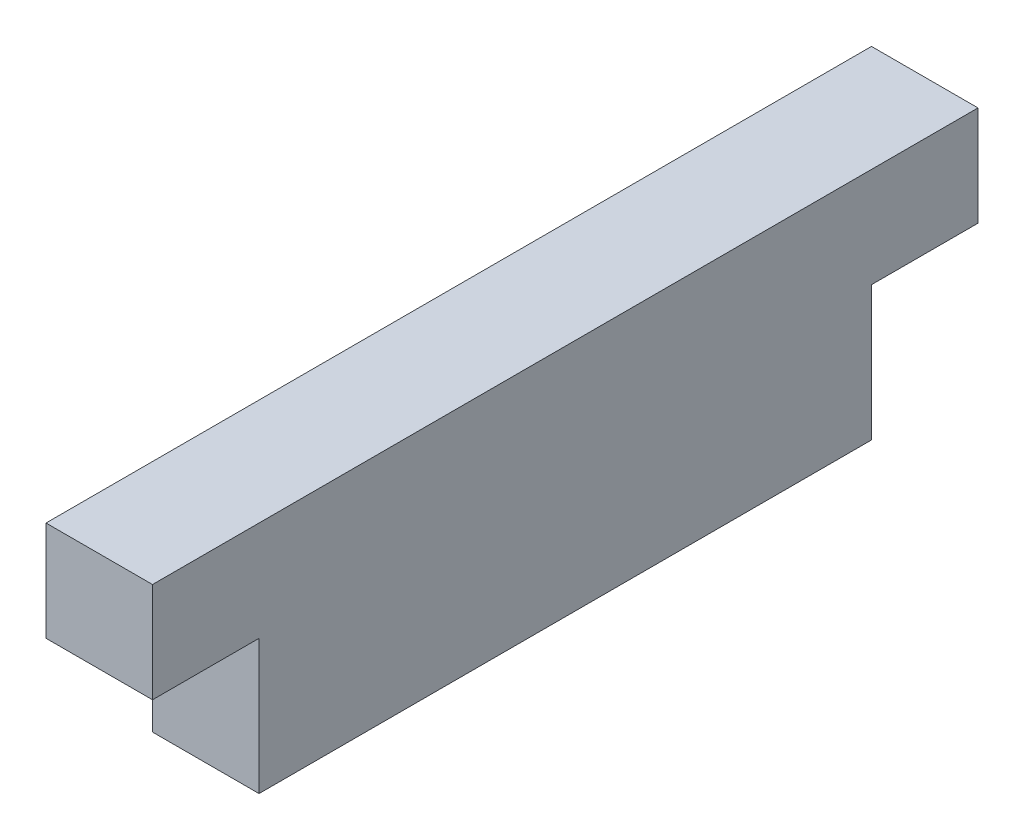
SolidWorks part; units mm, degrees
ref_plane "Front Plane" through (0, 0, 0) normal (0, 0, 1) x (1, 0, 0)
ref_plane "Top Plane" through (0, 0, 0) normal (0, 1, 0) x (1, 0, 0)
ref_plane "Right Plane" through (0, 0, 0) normal (1, 0, 0) x (0, 0, -1)
sketch "Sketch1" plane through (0, 0, 0) normal (1, 0, 0) x (0, 0, -1)
  line L0 (-14.605, -5.588) -> (14.605, -5.588)
  line L1 (-14.605, 5.588) -> (14.605, 5.588)
  line L2 (-14.605, 5.588) -> (-14.605, -5.588)
  line L4 (14.605, 5.588) -> (14.605, -5.588)
  line L5 (-14.605, 5.588) -> (14.605, -5.588) construction
  line L6 (-14.605, -5.588) -> (14.605, 5.588) construction
  line L12 (-14.605, 5.588) -> (-19.685, 5.588)
  line L13 (-14.605, 5.588) -> (-14.605, 0.8255)
  line L14 (-14.605, 0.8255) -> (-19.685, 0.8255)
  line L15 (-19.685, 5.588) -> (-19.685, 0.8255)
  line L16 (14.605, 5.588) -> (19.685, 5.588)
  line L17 (14.605, 5.588) -> (14.605, 0.8255)
  line L18 (14.605, 0.8255) -> (19.685, 0.8255)
  line L19 (19.685, 5.588) -> (19.685, 0.8255)
  point P0 (0, 0)
  dimension "D1" = 29.21
  dimension "D2" = 11.176
  dimension "D3" = 5.08
  dimension "D4" = 4.7625
extrude "Boss-Extrude1" add sketch "Sketch1" along normal blind 5.08
